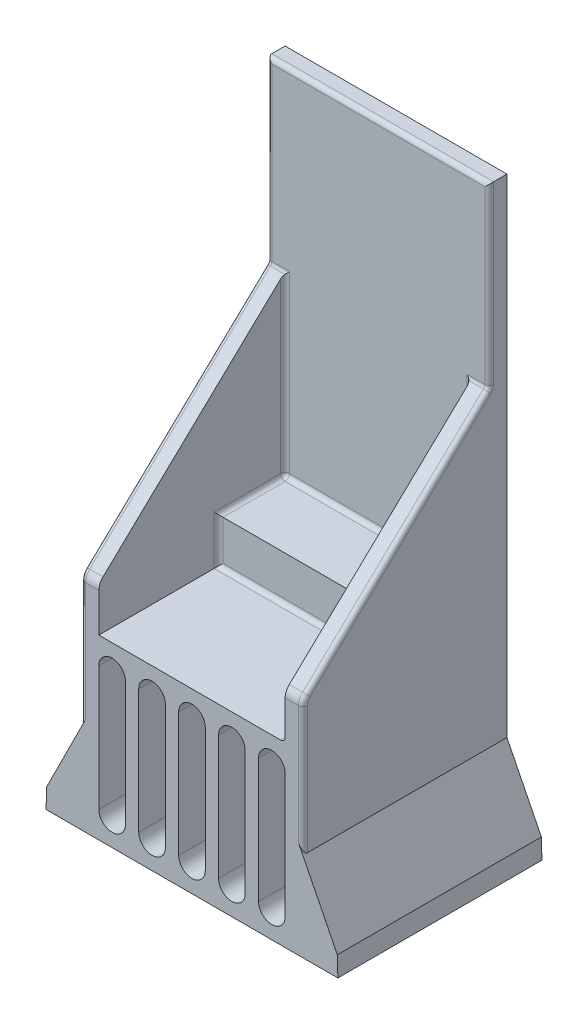
SolidWorks part; units mm, degrees
material "PLA-填充率10%"
ref_plane "前视基准面" through (0, 0, 0) normal (0, 0, 1) x (1, 0, 0)
ref_plane "上视基准面" through (0, 0, 0) normal (0, 1, 0) x (1, 0, 0)
ref_plane "右视基准面" through (0, 0, 0) normal (1, 0, 0) x (0, 0, -1)
sketch "草图1" plane through (0, 0, 0) normal (0, 1, 0) x (1, 0, 0)
  line L1 (-25, -25) -> (25, -25)
  line L2 (-25, -25) -> (-25, 25)
  line L3 (-25, 25) -> (25, 25)
  line L4 (25, -25) -> (25, 25)
  line L5 (-25, -25) -> (25, 25) construction
  line L6 (-25, 25) -> (25, -25) construction
  line L7 (25, -25) -> (-25, -25)
  line L8 (25, -25) -> (25, -21)
  line L9 (25, -21) -> (-25, -21)
  line L10 (-25, -25) -> (-25, -21)
  point P0 (0, 0)
  dimension "D1" = 50
  dimension "D2" = 50
  dimension "D3" = 4
extrude "凸台-拉伸1" add sketch "草图1" along normal blind 40 contours L9 L4 L3 L2
sketch "草图2" plane through (0, 40, 0) normal (0, 1, 0) x (1, 0, 0)
  line L0 (-25, -21) -> (25, -21)
  line L1 (-21, -21) -> (21, -21)
  line L2 (-21, -21) -> (-21, 21)
  line L3 (-21, 21) -> (21, 21)
  line L4 (21, -21) -> (21, 21)
  line L5 (-21, -21) -> (21, 21) construction
  line L6 (-21, 21) -> (21, -21) construction
  line L12 (-25, -21) -> (25, -21)
  line L13 (25, -21) -> (25, 25)
  line L18 (25, 25) -> (-25, 25)
  line L19 (-25, 25) -> (-25, -21)
  line L20 (-25, -21) -> (25, -21)
  line L21 (25, -21) -> (25, 25)
  line L22 (25, 25) -> (-25, 25)
  line L23 (-25, 25) -> (-25, -21)
  point P0 (0, 0)
  dimension "D1" = 42
  dimension "D2" = 42
  dimension "D3" = 0
extrude "凸台-拉伸2" add sketch "草图2" along normal blind 10
sketch "草图8" plane through (0, 0, -21) normal (0, 0, 1) x (1, 0, 0)
  line L4 (-21, 40) -> (21, 40)
  line L5 (21, 40) -> (21, 50)
  line L6 (21, 50) -> (-21, 50)
  line L7 (-21, 50) -> (-21, 40)
  line L8 (-21, 40) -> (21, 40)
  line L9 (21, 40) -> (21, 50)
  line L10 (21, 50) -> (-21, 50)
  line L11 (-21, 50) -> (-21, 40)
  dimension "D1" = 0
extrude "凸台-拉伸5" add sketch "草图8" along normal blind 15
sketch "草图3" plane through (0, 50, 0) normal (0, 1, 0) x (1, 0, 0)
  line L0 (25, -21) -> (25, 25) construction
  line L1 (-25, 25) -> (25, 25)
  line L2 (-25, 25) -> (-25, 21)
  line L3 (-25, 21) -> (25, 21)
  line L4 (25, 25) -> (25, 21)
  line L5 (-21, 21) -> (21, 21) construction
extrude "凸台-拉伸3" add sketch "草图3" along normal blind 80
sketch "草图4" plane through (0, 0, 0) normal (0, -1, 0) x (1, 0, 0)
  line L0 (25, 21) -> (25, -25) construction
  line L1 (-35, 21) -> (35, 21)
  line L2 (-35, 21) -> (-35, -25)
  line L3 (-35, -25) -> (35, -25)
  line L4 (35, 21) -> (35, -25)
  line L5 (-25, 21) -> (-25, -25) construction
  line L6 (-25, -25) -> (25, -25) construction
  line L7 (25, 21) -> (-25, 21) construction
  dimension "D1" = 10
  dimension "D2" = 10
  dimension "D3" = 0
  dimension "D4" = 0
ref_plane "基准面1" through (0, 20, 0) normal (0, 1, 0) x (1, 0, 0)
sketch "草图5" plane through (0, 20, 0) normal (0, 1, 0) x (1, 0, 0)
  line L4 (-25, -21) -> (25, -21)
  line L5 (-25, 25) -> (-25, -21)
  line L6 (25, 25) -> (-25, 25)
  line L7 (25, -21) -> (25, 25)
  line L8 (-25, -21) -> (25, -21)
  line L9 (-25, 25) -> (-25, -21)
  line L10 (25, 25) -> (-25, 25)
  line L11 (25, -21) -> (25, 25)
  dimension "D1" = 0
loft "放样2" add profiles "草图4", "草图5"
sketch "草图6" plane through (-25, 0, 0) normal (-1, 0, 0) x (0, 0, 1)
  line L0 (-21, 90) -> (21, 50)
  line L1 (-21, 130) -> (-21, 50) construction
  line L2 (21, 50) -> (-21, 50)
  line L3 (-21, 50) -> (21, 50) construction
  line L4 (-21, 50) -> (-21, 90)
  dimension "D1" = 40
extrude "凸台-拉伸4" add sketch "草图6" against normal blind 4
mirror "镜向2" about plane through (0, 0, 0) normal (1, 0, 0) of "凸台-拉伸4"
fillet "圆角2" radius 3 2 edges at (23, 50, 21) (-23, 50, 21)
chamfer "倒角1" distance 5 angle 25 2 edges
fillet "圆角4" radius 1 1 edges at (21, 40, 7.5)
sketch "草图7" plane through (0, 0, 21) normal (0, 0, 1) x (1, 0, 0)
  line L0 (0, 34) -> (0, 6) construction
  line L1 (3, 34) -> (3, 6)
  line L2 (-3, 34) -> (-3, 6)
  line L3 (25, 0) -> (-25, 0) construction
  line L4 (6, 34) -> (6, 6)
  line L5 (12, 34) -> (12, 6)
  line L6 (9, 34) -> (9, 6) construction
  line L7 (15, 34) -> (15, 6)
  line L8 (21, 34) -> (21, 6)
  line L9 (18, 34) -> (18, 6) construction
  line L10 (-3, 34) -> (-3, 6)
  line L11 (3, 34) -> (3, 6)
  line L12 (0, 34) -> (0, 6) construction
  line L13 (6, 34) -> (6, 6)
  line L14 (12, 34) -> (12, 6)
  line L15 (9, 34) -> (9, 6) construction
  line L16 (-12, 34) -> (-12, 6)
  line L17 (-6, 34) -> (-6, 6)
  line L18 (-9, 34) -> (-9, 6) construction
  line L19 (-3, 34) -> (-3, 6)
  line L20 (3, 34) -> (3, 6)
  line L21 (0, 34) -> (0, 6) construction
  line L22 (-12, 34) -> (-12, 6)
  line L23 (-6, 34) -> (-6, 6)
  line L24 (-9, 34) -> (-9, 6) construction
  line L25 (-21, 34) -> (-21, 6)
  line L26 (-15, 34) -> (-15, 6)
  line L27 (-18, 34) -> (-18, 6) construction
  arc A0 (3, 34) -> (-3, 34) centre (0, 34) ccw
  arc A1 (-3, 6) -> (3, 6) centre (0, 6) ccw
  arc A2 (12, 34) -> (6, 34) centre (9, 34) ccw
  arc A3 (6, 6) -> (12, 6) centre (9, 6) ccw
  arc A4 (21, 34) -> (15, 34) centre (18, 34) ccw
  arc A5 (15, 6) -> (21, 6) centre (18, 6) ccw
  arc A6 (3, 34) -> (-3, 34) centre (0, 34) ccw
  arc A7 (-3, 6) -> (3, 6) centre (0, 6) ccw
  arc A8 (12, 34) -> (6, 34) centre (9, 34) ccw
  arc A9 (6, 6) -> (12, 6) centre (9, 6) ccw
  arc A10 (-6, 34) -> (-12, 34) centre (-9, 34) ccw
  arc A11 (-12, 6) -> (-6, 6) centre (-9, 6) ccw
  arc A12 (3, 34) -> (-3, 34) centre (0, 34) ccw
  arc A13 (-3, 6) -> (3, 6) centre (0, 6) ccw
  arc A14 (-6, 34) -> (-12, 34) centre (-9, 34) ccw
  arc A15 (-12, 6) -> (-6, 6) centre (-9, 6) ccw
  arc A16 (-15, 34) -> (-21, 34) centre (-18, 34) ccw
  arc A17 (-21, 6) -> (-15, 6) centre (-18, 6) ccw
  point P3 (0, 20)
  point P15 (9, 20)
  point P22 (18, 20)
  point P29 (0, 20)
  point P36 (9, 20)
  point P43 (-9, 20)
  point P50 (0, 20)
  point P57 (-9, 20)
  point P64 (-18, 20)
  dimension "D1" = 3
  dimension "D3" = 6
  dimension "D2" = 28
  dimension "D4" = 3
  dimension "D5" = 3
extrude "切除-拉伸1" cut sketch "草图7" against normal through all contours L25 A17 L26 A16 | L16 A11 L17 A10 | L2 A1 L1 A0 | L4 A3 L5 A2 | L7 A5 L8 A4
fillet "圆角5" radius 1 19 edges at (-25, 49.896, 20.7574) (25, 49.896, 20.7574) (-25, 70.4433, -0.4655) (25, 70.4433, -0.4655) (-0.5, 40, -6) (20.7071, 40.2929, -6) (21, 70, -21) (0, 50, -21) (-21, 70, -21) (-23, 90, -21) (-25, 110, -21) (0, 130, -21) (25, 110, -21) (23, 90, -21) (-21, 50, -13.5) (-21, 45, -6) (21, 45.5, -6)
